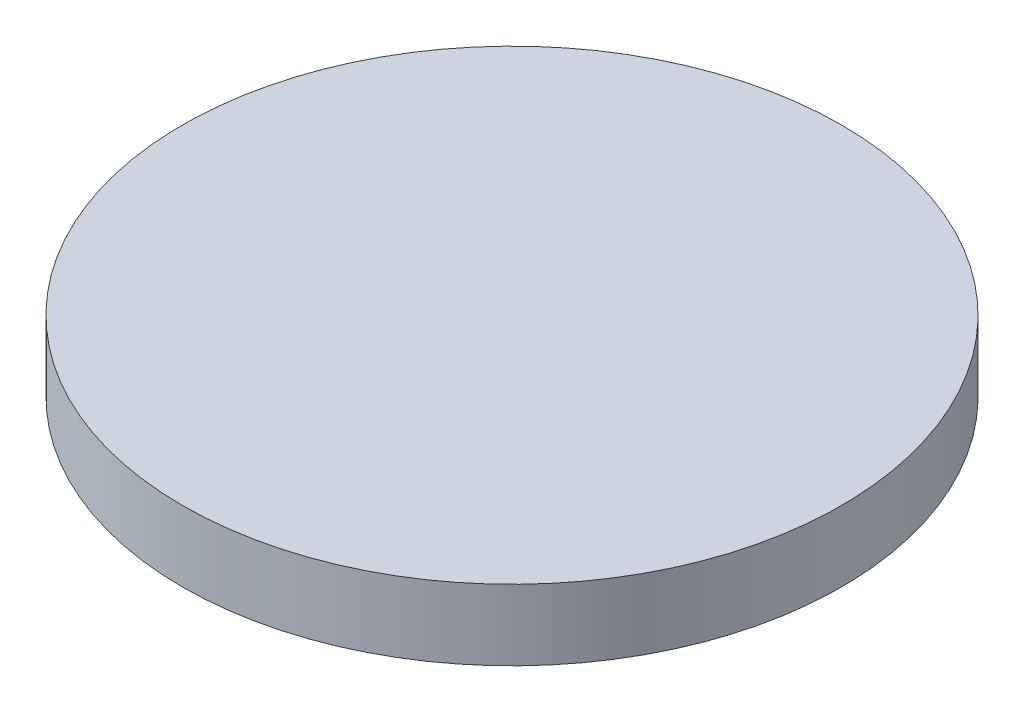
SolidWorks part; units mm, degrees
ref_plane "Front Plane" through (0, 0, 0) normal (0, 0, 1) x (1, 0, 0)
ref_plane "Top Plane" through (0, 0, 0) normal (0, 1, 0) x (1, 0, 0)
ref_plane "Right Plane" through (0, 0, 0) normal (1, 0, 0) x (0, 0, -1)
sketch "Sketch1" plane through (0, 0, 0) normal (0, 1, 0) x (1, 0, 0)
  circle A0 centre (0, 0) radius 44.45
  dimension "D1" = 88.9
extrude "Boss-Extrude1" add sketch "Sketch1" along normal mid plane 9.525
